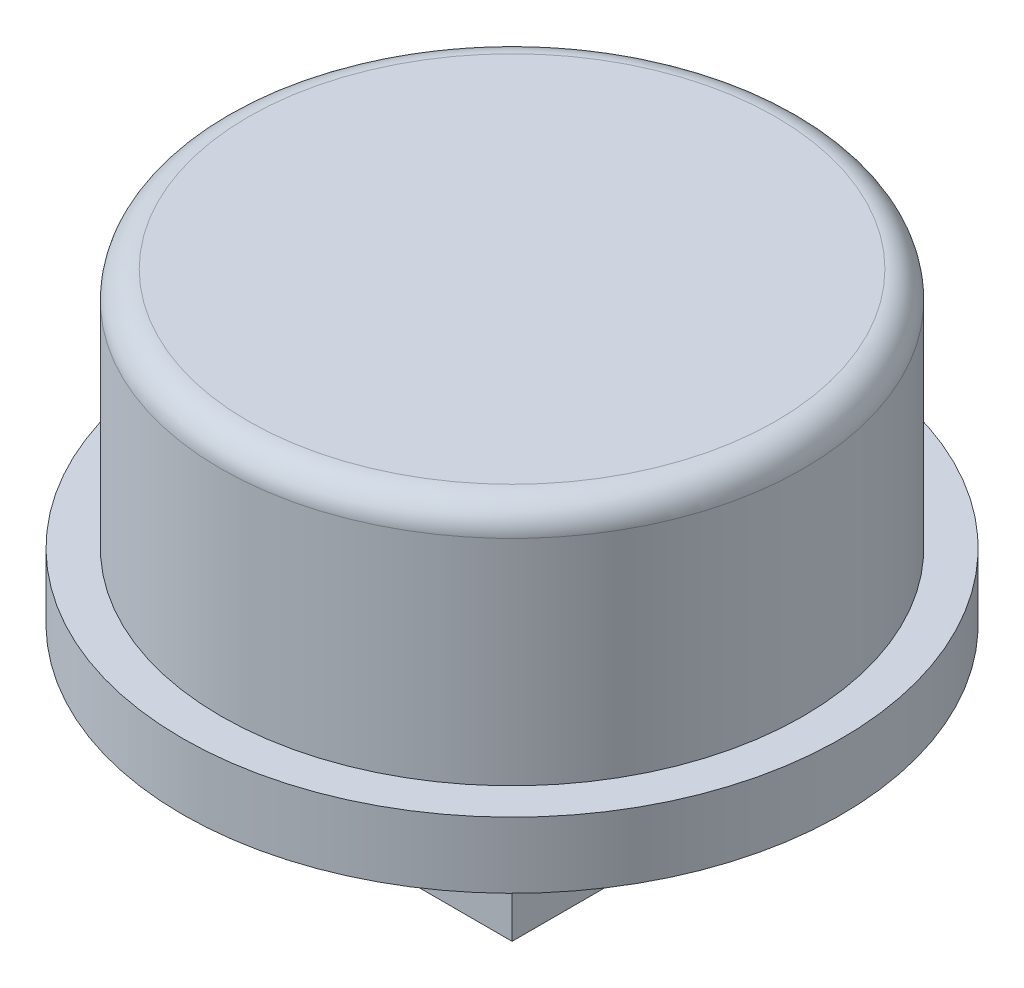
SolidWorks part; units mm, degrees
material "PBT General Purpose"
ref_plane "Front Plane" through (0, 0, 0) normal (0, 0, 1) x (1, 0, 0)
ref_plane "Top Plane" through (0, 0, 0) normal (0, 1, 0) x (1, 0, 0)
ref_plane "Right Plane" through (0, 0, 0) normal (1, 0, 0) x (0, 0, -1)
sketch "Sketch2" plane through (0, 0, 0) normal (0, 1, 0) x (1, 0, 0)
  circle A0 centre (0, 0) radius 6
  dimension "D1" = 12
extrude "Boss-Extrude1" add sketch "Sketch2" along normal blind 5.6
sketch "Sketch3" plane through (0, 5.6, 0) normal (0, 1, 0) x (1, 0, 0)
  circle A0 centre (0, 0) radius 6
  circle A1 centre (0, 0) radius 5.3
  circle A2 centre (0, 0) radius 6 construction
  point P4 (0, 6)
  point P5 (0, 6)
  point P6 (0, 6)
  dimension "D1" = 0.7
extrude "Cut-Extrude1" cut sketch "Sketch3" against normal blind 4.4
fillet "Fillet1" radius 0.5 1 edges at (0, 5.6, 5.3)
sketch "Sketch4" plane through (0, 0, 0) normal (0, -1, 0) x (1, 0, 0)
  line L1 (-2, -2) -> (2, -2)
  line L2 (-2, -2) -> (-2, 2)
  line L3 (-2, 2) -> (2, 2)
  line L4 (2, -2) -> (2, 2)
  line L5 (-2, -2) -> (2, 2) construction
  line L6 (-2, 2) -> (2, -2) construction
  line L7 (-2.5, -2.5) -> (2.5, -2.5)
  line L8 (-2.5, -2.5) -> (-2.5, 2.5)
  line L9 (-2.5, 2.5) -> (2.5, 2.5)
  line L10 (2.5, -2.5) -> (2.5, 2.5)
  line L11 (-2.5, -2.5) -> (2.5, 2.5) construction
  line L12 (-2.5, 2.5) -> (2.5, -2.5) construction
  point P0 (0, 0)
  point P6 (0, 0)
  dimension "D1" = 4
  dimension "D2" = 0.5
extrude "Boss-Extrude2" add sketch "Sketch4" along normal blind 2.5
